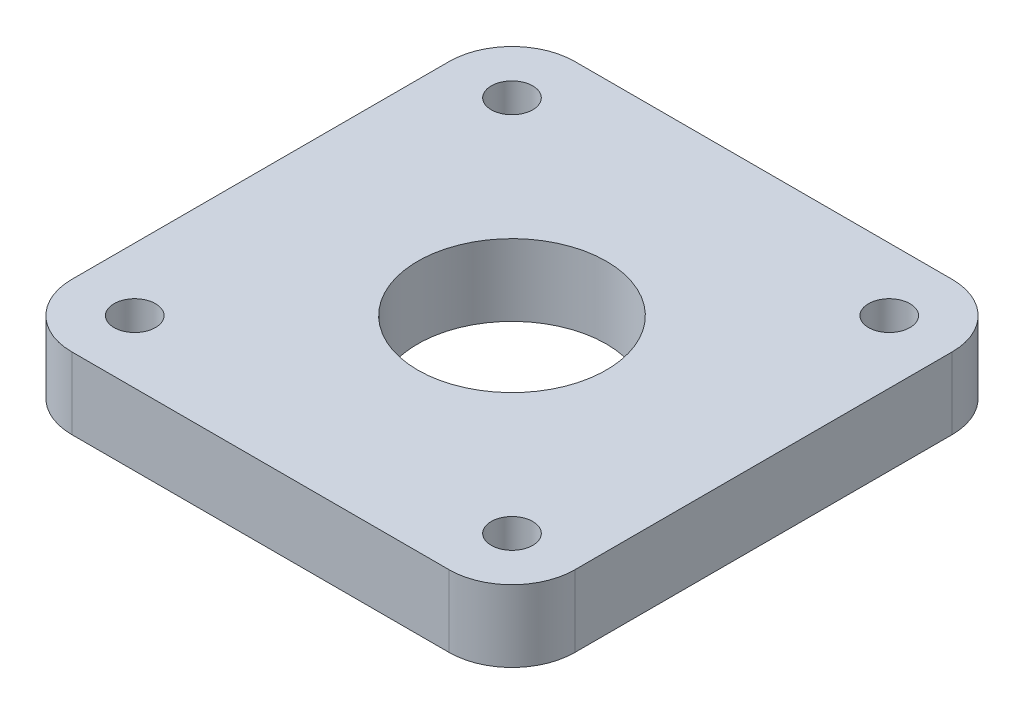
SolidWorks part; units mm, degrees
ref_plane "Front Plane" through (0, 0, 0) normal (0, 0, 1) x (1, 0, 0)
ref_plane "Top Plane" through (0, 0, 0) normal (0, 1, 0) x (1, 0, 0)
ref_plane "Right Plane" through (0, 0, 0) normal (1, 0, 0) x (0, 0, -1)
sketch "Sketch1" plane through (0, 0, 0) normal (0, 1, 0) x (1, 0, 0)
  line L1 (-15, -20) -> (15, -20)
  line L2 (-20, -15) -> (-20, 15)
  line L3 (-15, 20) -> (15, 20)
  line L4 (20, -15) -> (20, 15)
  line L5 (-20, -20) -> (20, 20) construction
  line L6 (-20, 20) -> (20, -20) construction
  arc A0 (15, -20) -> (20, -15) centre (15, -15) ccw
  arc A1 (-15, -20) -> (-20, -15) centre (-15, -15) cw
  arc A2 (-20, 15) -> (-15, 20) centre (-15, 15) cw
  arc A3 (15, 20) -> (20, 15) centre (15, 15) cw
  point P0 (0, 0)
  dimension "D3" = 5
  dimension "D1" = 40
  dimension "D2" = 40
extrude "Boss-Extrude1" add sketch "Sketch1" along normal blind 5.7
sketch "Sketch2" plane through (0, 5.7, 0) normal (0, 1, 0) x (1, 0, 0)
  line L0 (-20, 15) -> (-15, 15) construction
  line L1 (-20, 15) -> (-20, -15) construction
  line L2 (-15, 15) -> (-15, 20) construction
  line L3 (15, 20) -> (-15, 20) construction
  line L4 (0, 20) -> (0, -20) construction
  line L5 (-15, -20) -> (15, -20) construction
  line L6 (-20, 0) -> (20, 0) construction
  line L7 (20, -15) -> (20, 15) construction
  circle A0 centre (0, 0) radius 7.5
  circle A1 centre (-15, 15) radius 1.65
  circle A2 centre (15, 15) radius 1.65
  circle A3 centre (15, -15) radius 1.65
  circle A4 centre (-15, -15) radius 1.65
  dimension "D1" = 15
  dimension "D4" = 3.3
  dimension "D2" = 5
  dimension "D3" = 5
extrude "Cut-Extrude1" cut sketch "Sketch2" against normal through all
